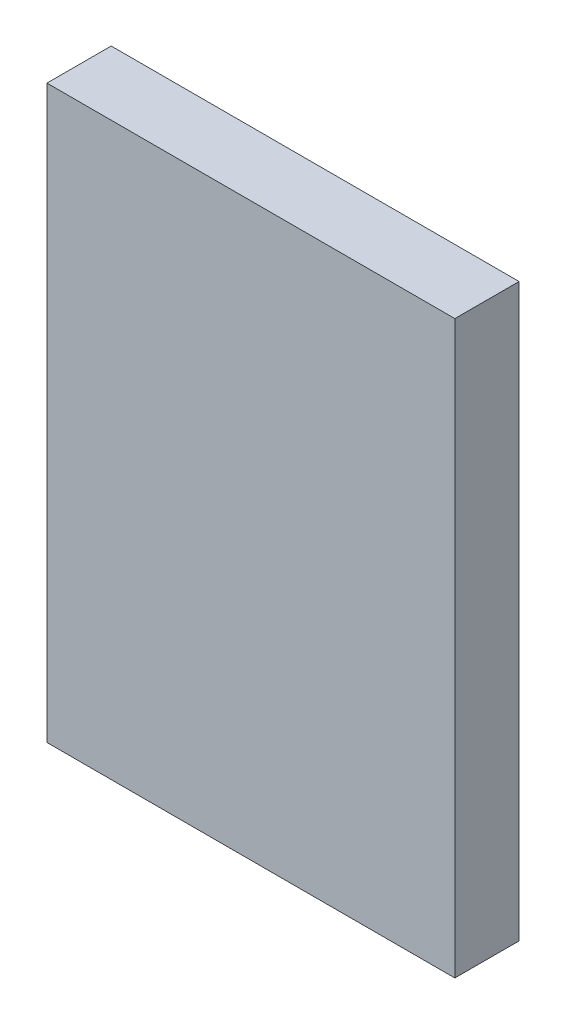
SolidWorks part; units mm, degrees
ref_plane "Front Plane" through (0, 0, 0) normal (0, 0, 1) x (1, 0, 0)
ref_plane "Top Plane" through (0, 0, 0) normal (0, 1, 0) x (1, 0, 0)
ref_plane "Right Plane" through (0, 0, 0) normal (1, 0, 0) x (0, 0, -1)
sketch "Sketch1" plane through (0, 0, 0) normal (0, 0, 1) x (1, 0, 0)
  line L0 (-3.175, 4.445) -> (3.175, 4.445)
  line L1 (3.175, 4.445) -> (3.175, -4.445)
  line L2 (3.175, -4.445) -> (-3.175, -4.445)
  line L3 (-3.175, -4.445) -> (-3.175, 4.445)
extrude "Component_Outline" add sketch "Sketch1" along normal blind 1 separate body
sketch3d "3DSketch1"
  line L0 (0, 0, 0) -> (1, 0, 0)
  line L1 (0, 0, 0) -> (0, 1, 0)
  line L2 (0, 0, 0) -> (0, 0, 1)
  point P0 (0, 0, 0)
